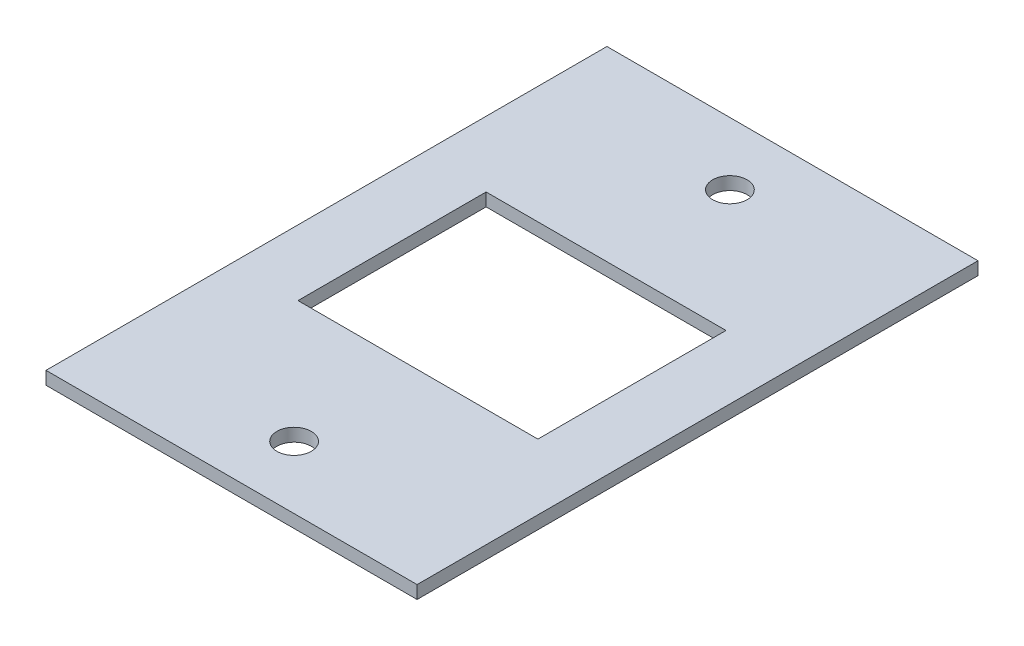
SolidWorks part; units mm, degrees
ref_plane "Спереди" through (0, 0, 0) normal (0, 0, 1) x (1, 0, 0)
ref_plane "Сверху" through (0, 0, 0) normal (0, 1, 0) x (1, 0, 0)
ref_plane "Справа" through (0, 0, 0) normal (1, 0, 0) x (0, 0, -1)
sketch "Эскиз1" plane through (0, 0, 0) normal (0, 1, 0) x (1, 0, 0)
  line L0 (21.5, 21.6) -> (21.5, 0) construction
  line L1 (0, 0) -> (43, 0)
  line L2 (0, 0) -> (0, 65)
  line L3 (0, 65) -> (43, 65)
  line L4 (43, 0) -> (43, 65)
  line L5 (0, 32.5) -> (43, 32.5) construction
  line L6 (7.6, 43.4) -> (35.4, 43.4)
  line L8 (7.6, 43.4) -> (7.6, 21.6)
  line L9 (7.6, 21.6) -> (35.4, 21.6)
  line L10 (35.4, 43.4) -> (35.4, 21.6)
  circle A0 centre (21.5, 7.25) radius 2
  circle A1 centre (21.5, 57.75) radius 2
  point P25 (35.4, 32.5)
  point P26 (7.6, 32.5)
extrude "Бобышка-Вытянуть1" add sketch "Эскиз1" along normal blind 1.5
